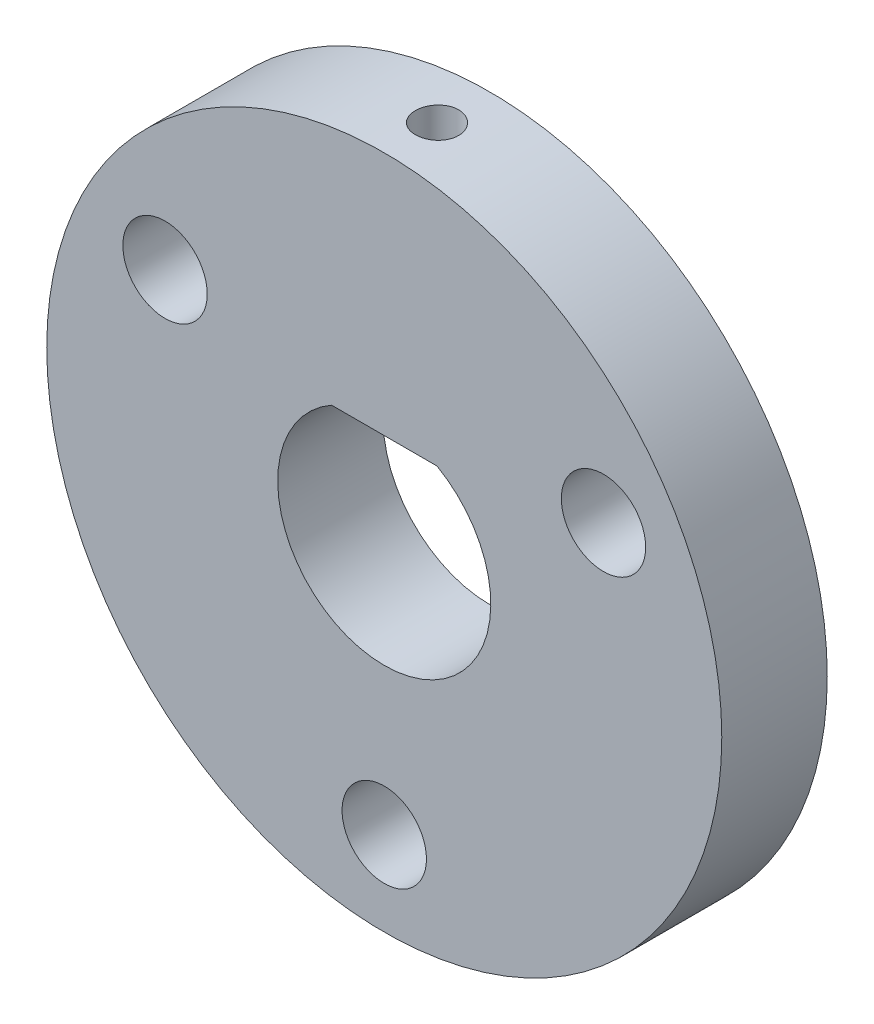
SolidWorks part; units mm, degrees
material "Plain Carbon Steel"
ref_plane "Front Plane" through (0, 0, 0) normal (0, 0, 1) x (1, 0, 0)
ref_plane "Top Plane" through (0, 0, 0) normal (0, 1, 0) x (1, 0, 0)
ref_plane "Right Plane" through (0, 0, 0) normal (1, 0, 0) x (0, 0, -1)
sketch "Sketch1" plane through (0, 0, 0) normal (0, 0, 1) x (1, 0, 0)
  line L0 (-2.5, 4.3878) -> (2.5, 4.3878)
  line L1 (-2.5, 4.3301) -> (2.5, 4.3301) construction
  circle A0 centre (0, 0) radius 5.05
  circle A1 centre (0, 0) radius 12 construction
  circle A2 centre (0, 0) radius 16
  circle A3 centre (0, 0) radius 5 construction
  dimension "D1" = 10.1
  dimension "D3" = 24
  dimension "D4" = 32
  dimension "D6" = 10
  dimension "D2" = 5
  dimension "D5" = 5
extrude "Boss-Extrude1" add sketch "Sketch1" along normal mid plane 5 contours A2 A0 | L0 A0
hole_wizard "M4 Clearance Hole1" positions "Sketch2" profile "Sketch3" hole size "M4" standard "ANSI Metric"
sketch "Sketch2" plane through (0, 0, 2.5) normal (0, 0, 1) x (1, 0, 0)
  circle A0 centre (0, 0) radius 12 construction
  point P0 (0, 12)
  point P4 (12, 0)
  point P6 (0, -12)
  point P8 (-12, 0)
sketch "Sketch3" plane through (0, 12, 2.5) normal (1, 0, 0) x (0, -1, 0)
  line L0 (0, 0) -> (0, 5)
  line L1 (0, 5) -> (2, 5)
  line L2 (2, 5) -> (2, 0)
  line L5 (2, 0) -> (0, 0)
  line L11 (0, -6.35) -> (0, 107.95) construction
  dimension "Thru Hole Dia." = 4
  dimension "Thru Hole Depth" = 5
hole_wizard "M4 Clearance Hole2" positions "Sketch4" profile "Sketch5" hole size "M4" standard "ANSI Metric" end condition through all
sketch "Sketch4" plane through (0, 0, 2.5) normal (0, 0, 1) x (1, 0, 0)
  circle A0 centre (0, 0) radius 12 construction
  point P0 (0, -12)
sketch "Sketch5" plane through (0, -12, 2.5) normal (1, 0, 0) x (0, -1, 0)
  line L0 (0, 0) -> (0, 5)
  line L1 (0, 5) -> (2, 5)
  line L2 (2, 5) -> (2, 0)
  line L5 (2, 0) -> (0, 0)
  line L11 (0, -6.35) -> (0, 107.95) construction
  dimension "Thru Hole Dia." = 4
  dimension "Thru Hole Depth" = 5
pattern_circular "CirPattern1" count 3 over 360 about axis through (0, 0, 0) along (0, 0, 1) of "M4 Clearance Hole2"
hole_wizard "M2.5x0.45 Tapped Hole1" positions "Sketch6" profile "Sketch7" tap size "M2.5x0.45" standard "ANSI Metric"
sketch "Sketch6" plane through (0, 4.3878, 0) normal (0, -1, 0) x (-1, 0, 0)
  point P0 (0, 0)
sketch "Sketch7" plane through (0, 4.3878, 0) normal (1, 0, 0) x (0, 0, -1)
  line L0 (0, 0) -> (0, 11.6122)
  line L1 (0, 11.6122) -> (1.025, 11.6122)
  line L2 (1.025, 11.6122) -> (1.025, 0)
  line L5 (1.025, 0) -> (0, 0)
  line L11 (0, -6.35) -> (0, 107.95) construction
  dimension "Thru Tap Drill Dia." = 2.05
  dimension "Thru Tap Drill Depth" = 11.6122
cosmetic thread "Hole Thread1" parameters "D2"=2.5
